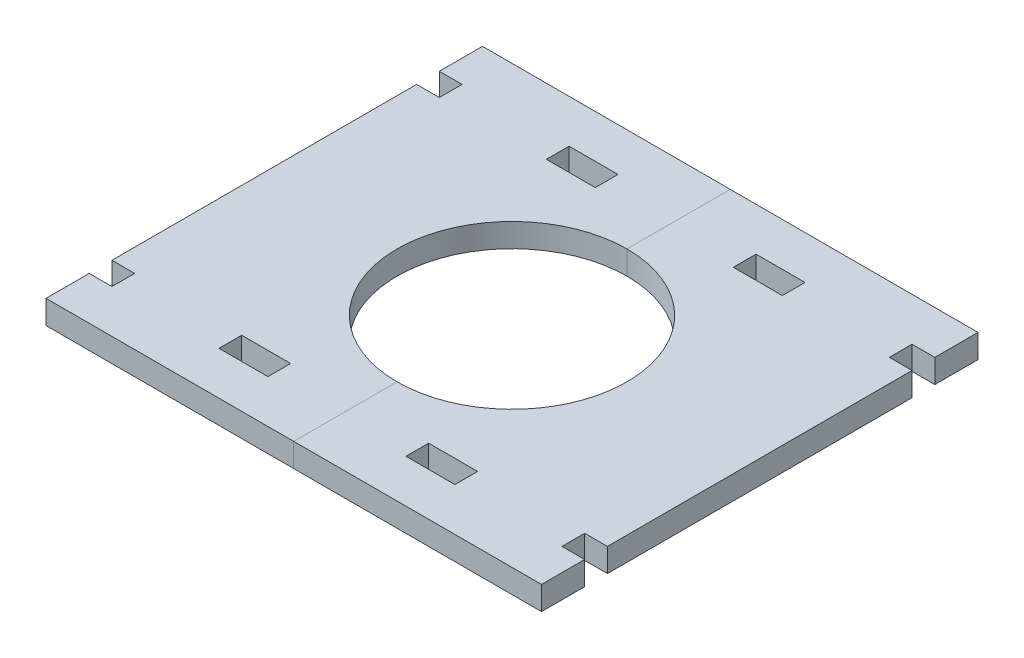
SolidWorks part; units mm, degrees
ref_plane "Front Plane" through (0, 0, 0) normal (0, 0, 1) x (1, 0, 0)
ref_plane "Top Plane" through (0, 0, 0) normal (0, 1, 0) x (1, 0, 0)
ref_plane "Right Plane" through (0, 0, 0) normal (1, 0, 0) x (0, 0, -1)
sketch "Sketch1" plane through (0, 0, 0) normal (0, 1, 0) x (1, 0, 0)
  circle A2 centre (0, 0) radius 19.5
  dimension "D1" = 39
sketch "Sketch2" plane through (0, 0, 0) normal (0, 1, 0) x (1, 0, 0)
  line L17 (-42, -37) -> (42, -37)
  line L18 (-42, -37) -> (-42, 37)
  line L19 (-42, 37) -> (42, 37)
  line L20 (42, -37) -> (42, 37)
  circle A15 centre (0, 0) radius 19.5
  circle A16 centre (0, 0) radius 19.5
  point P0 (42, 0)
  point P1 (0, 37)
  dimension "D1" = 84
  dimension "D2" = 74
  dimension "D3" = 0
extrude "Boss-Extrude1" add sketch "Sketch2" along normal blind 4
split "Split1" trim tools "Right Plane" bodies to split 101 resulting bodies 102 103
sketch "Sketch4" plane through (0, 4, 0) normal (0, 1, 0) x (1, 0, 0)
  line L0 (0, -18.5) -> (42, -18.5) construction
  line L2 (42, -37) -> (42, 37) construction
  line L3 (0, -18.5) -> (0, -37) construction
  line L4 (-42, -37) -> (-42, 37) construction
  line L5 (-20, -29.675) -> (-11.7, -29.675)
  line L6 (-20, -29.675) -> (-20, -25.825)
  line L7 (-20, -25.825) -> (-11.7, -25.825)
  line L8 (-11.7, -29.675) -> (-11.7, -25.825)
  line L9 (-20, -29.675) -> (-11.7, -25.825) construction
  line L10 (-20, -25.825) -> (-11.7, -29.675) construction
  line L11 (-42, -29.675) -> (-38.15, -29.675)
  line L12 (-42, -29.675) -> (-42, -25.825)
  line L13 (-42, -25.825) -> (-38.15, -25.825)
  line L14 (-38.15, -29.675) -> (-38.15, -25.825)
  line L15 (-42, -29.675) -> (-38.15, -25.825) construction
  line L16 (-42, -25.825) -> (-38.15, -29.675) construction
  line L17 (0, 0) -> (0, -37) construction
  line L33 (42, -25.825) -> (38.15, -29.675) construction
  line L34 (42, -29.675) -> (38.15, -25.825) construction
  line L35 (20, -25.825) -> (11.7, -29.675) construction
  line L36 (20, -29.675) -> (11.7, -25.825) construction
  line L45 (38.15, -29.675) -> (38.15, -25.825)
  line L46 (42, -25.825) -> (38.15, -25.825)
  line L47 (42, -29.675) -> (42, -25.825)
  line L48 (42, -29.675) -> (38.15, -29.675)
  line L49 (11.7, -29.675) -> (11.7, -25.825)
  line L50 (20, -25.825) -> (11.7, -25.825)
  line L51 (20, -29.675) -> (20, -25.825)
  line L52 (20, -29.675) -> (11.7, -29.675)
  line L53 (-2.2, 0) -> (2.2, 0) construction
  line L54 (20, 29.675) -> (11.7, 25.825) construction
  line L55 (20, 25.825) -> (11.7, 29.675) construction
  line L56 (42, 29.675) -> (38.15, 25.825) construction
  line L57 (42, 25.825) -> (38.15, 29.675) construction
  line L58 (20, 29.675) -> (11.7, 29.675)
  line L59 (20, 29.675) -> (20, 25.825)
  line L60 (20, 25.825) -> (11.7, 25.825)
  line L61 (11.7, 29.675) -> (11.7, 25.825)
  line L62 (42, 29.675) -> (38.15, 29.675)
  line L63 (42, 29.675) -> (42, 25.825)
  line L64 (42, 25.825) -> (38.15, 25.825)
  line L65 (38.15, 29.675) -> (38.15, 25.825)
  line L82 (-42, 25.825) -> (-38.15, 29.675) construction
  line L83 (-42, 29.675) -> (-38.15, 25.825) construction
  line L84 (-20, 25.825) -> (-11.7, 29.675) construction
  line L85 (-20, 29.675) -> (-11.7, 25.825) construction
  line L94 (-38.15, 29.675) -> (-38.15, 25.825)
  line L95 (-42, 25.825) -> (-38.15, 25.825)
  line L96 (-42, 29.675) -> (-42, 25.825)
  line L97 (-42, 29.675) -> (-38.15, 29.675)
  line L98 (-11.7, 29.675) -> (-11.7, 25.825)
  line L99 (-20, 25.825) -> (-11.7, 25.825)
  line L100 (-20, 29.675) -> (-20, 25.825)
  line L101 (-20, 29.675) -> (-11.7, 29.675)
  point P6 (-15.85, -27.75)
  point P14 (0, -27.75)
  point P15 (-40.075, -27.75)
  point P53 (40.075, -27.75)
  point P54 (15.85, -27.75)
  point P65 (15.85, 27.75)
  point P66 (40.075, 27.75)
  point P95 (-40.075, 27.75)
  point P96 (-15.85, 27.75)
  dimension "D1" = 3.85
  dimension "D2" = 8.3
  dimension "D3" = 20
  dimension "D4" = 3.85
extrude "Cut-Extrude2" cut sketch "Sketch4" against normal through all both
equation "\"m3_hole\"= 3.5"
equation "\"m3_washer\"= 7.3"
equation "\"m3_nut\"= 5.3"
equation "\"guide_width\"= 10.0"
equation "\"guide_length\"= 65.0"
equation "\"guide_tab_length\" = 10.0"
equation "\"guide_tab_width\" = 9.0"
equation "\"guide_thickness\" = 12.0"
equation "\"grinder_od\"= 52.0"
equation "\"grinder_id\"= 45.5"
equation "\"grinder_adjust_od\" = 58.0"
equation "\"funnel_width_from_adjust_ring\" = 13.0"
equation "\"drill_contact_diameter_small\" = 24.0"
equation "\"drill_contact_diameter_medium\" = 28.0"
equation "\"drill_contact_diameter_large\" = 39.0"
equation "\"drill_contact_diameter_tab\" = 31.0"
equation "\"drill_contact_ow_tab\" = 14.5"
equation "\"drill_contact_iw_tab\" = 8.7"
equation "\"drill_contact_small_height\" = 15.5"
equation "\"drill_contact_large_height\" = 34.5"
equation "\"D1@Sketch2\"=\"grinder_od\"+\"guide_thickness\"+20"
equation "\"D2@Sketch2\"=\"grinder_od\"+\"guide_thickness\"+\"guide_tab_length\""
equation "\"plywood_thickness\" = 3.85"
equation "\"plywood_peg_length\" = 40"
equation "\"plywood_peg_width\" = 8.3"
equation "\"D3@Sketch4\"=\"plywood_peg_length\"/2"
equation "\"D2@Sketch4\"=\"plywood_peg_width\""
equation "\"D1@Sketch4\"=\"plywood_thickness\""
equation "\"D4@Sketch4\"=\"plywood_thickness\""
equation "\"D1@Sketch1\"=\"drill_contact_diameter_large\""
